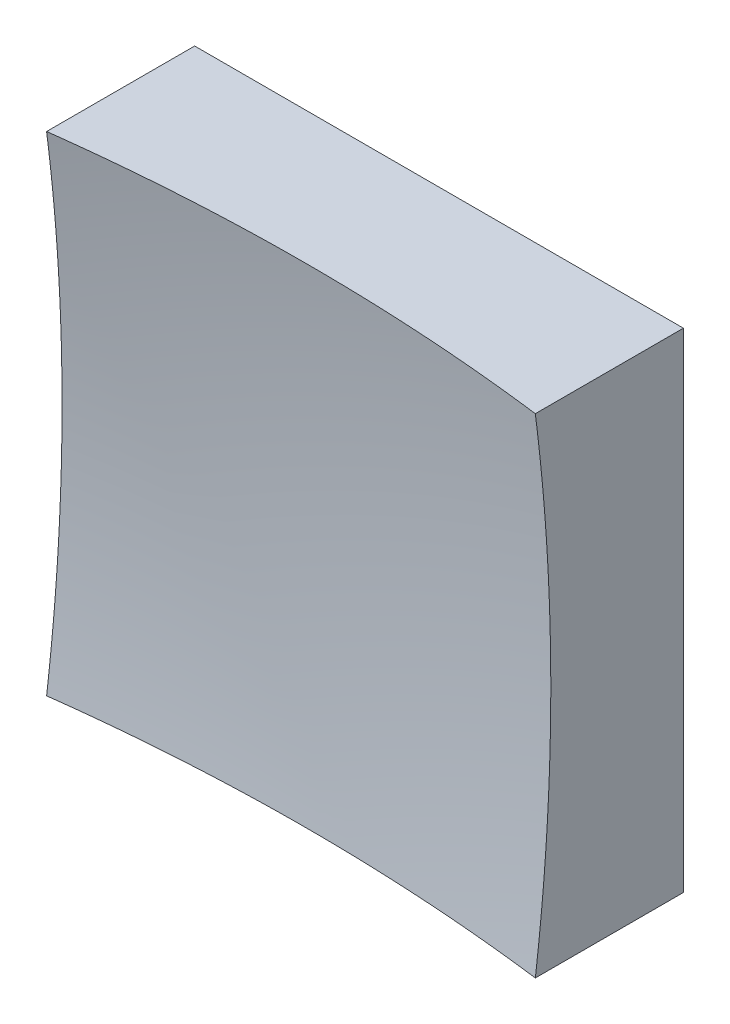
SolidWorks part; units mm, degrees
ref_plane "前视基准面" through (0, 0, 0) normal (0, 0, 1) x (1, 0, 0)
ref_plane "上视基准面" through (0, 0, 0) normal (0, 1, 0) x (1, 0, 0)
ref_plane "右视基准面" through (0, 0, 0) normal (1, 0, 0) x (0, 0, -1)
sketch "草图1" plane through (0, 0, 0) normal (0, 0, 1) x (1, 0, 0)
  line L1 (-6.25, 6.25) -> (6.25, 6.25)
  line L2 (-6.25, 6.25) -> (-6.25, -6.25)
  line L3 (-6.25, -6.25) -> (6.25, -6.25)
  line L4 (6.25, 6.25) -> (6.25, -6.25)
  line L5 (-6.25, 6.25) -> (6.25, -6.25) construction
  line L6 (-6.25, -6.25) -> (6.25, 6.25) construction
  point P0 (0, 0)
  dimension "D1" = 12.5
  dimension "D2" = 12.5
extrude "凸台-拉伸1" add sketch "草图1" along normal blind 10 contours L2 L3 L4 L1
sketch "草图2" plane through (0, 0, 0) normal (0, 1, 0) x (1, 0, 0)
  line L0 (-7.4603, -3) -> (7.3192, -3) construction
  line L1 (0, 0) -> (0, -12.1749) construction
  line L2 (48.7423, -41.8559) -> (0, -41.8559)
  line L3 (0, -41.8559) -> (0, -3)
  arc A1 (48.7423, -41.8559) -> (0, -3) centre (0, -53) ccw
  dimension "D2" = 100
  dimension "D1" = 3
revolve "切除-旋转2" cut sketch "草图2" angle 360 about L3
